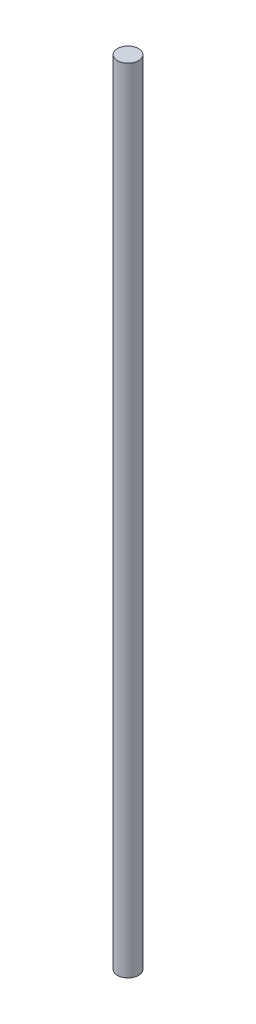
SolidWorks part; units mm, degrees
ref_plane "Alzado" through (0, 0, 0) normal (0, 0, 1) x (1, 0, 0)
ref_plane "Planta" through (0, 0, 0) normal (0, 1, 0) x (1, 0, 0)
ref_plane "Vista lateral" through (0, 0, 0) normal (1, 0, 0) x (0, 0, -1)
sketch "Croquis1" plane through (0, 0, 0) normal (0, 1, 0) x (1, 0, 0)
  circle A0 centre (0, 0) radius 4
  dimension "D1" = 8
extrude "Saliente-Extruir1" add sketch "Croquis1" along normal blind 300
